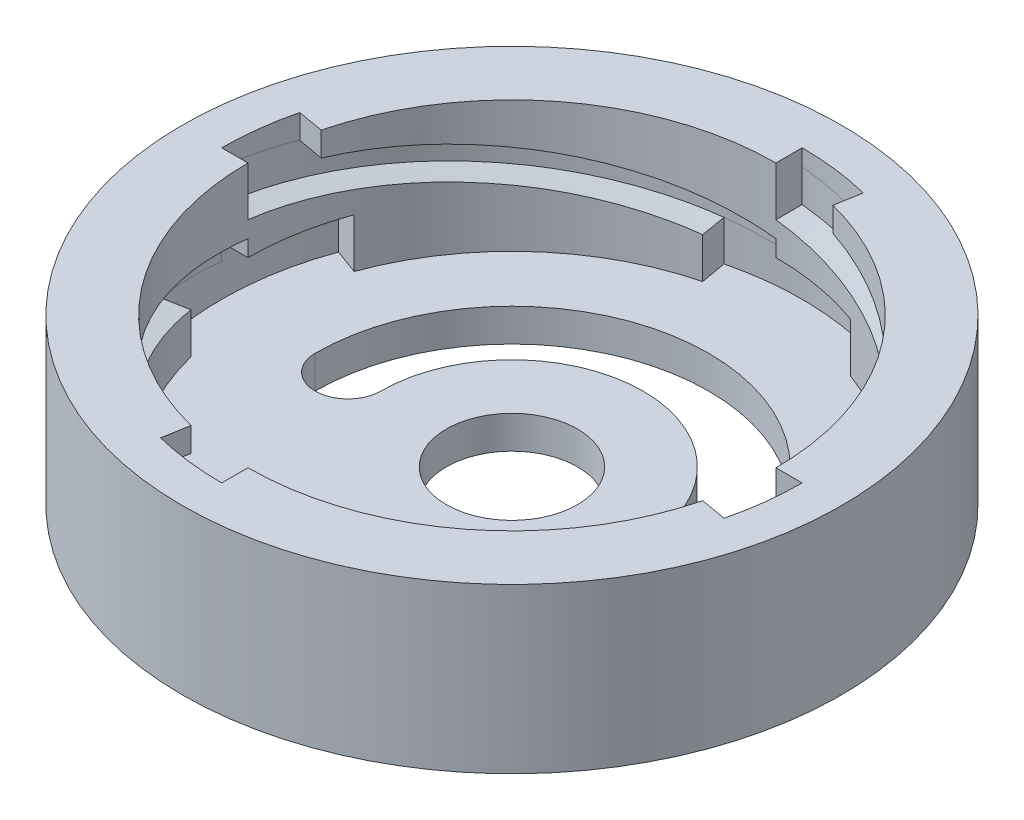
SolidWorks part; units mm, degrees
ref_plane "Front Plane" through (0, 0, 0) normal (0, 0, 1) x (1, 0, 0)
ref_plane "Top Plane" through (0, 0, 0) normal (0, 1, 0) x (1, 0, 0)
ref_plane "Right Plane" through (0, 0, 0) normal (1, 0, 0) x (0, 0, -1)
sketch "Sketch1" plane through (0, 0, 0) normal (0, 1, 0) x (1, 0, 0)
  line L0 (-10, 0) -> (10, 0) construction
  circle A0 centre (0, 0) radius 16.1
  circle A1 centre (0, 0) radius 4
  arc A2 (-10, 0) -> (10, 0) centre (0, 0) cw construction
  arc A3 (12, 0) -> (-12, 0) centre (0, 0) ccw
  arc A4 (8, 0) -> (-8, 0) centre (0, 0) ccw
  arc A5 (8, 0) -> (12, 0) centre (10, 0) ccw
  arc A6 (-12, 0) -> (-8, 0) centre (-10, 0) ccw
  point P6 (0, 10)
  dimension "D1" = 32.2
  dimension "D2" = 2
  dimension "D3" = 8
  dimension "D4" = 10
extrude "Boss-Extrude1" add sketch "Sketch1" along normal blind 2
sketch "Sketch2" plane through (0, 0, 0) normal (0, 1, 0) x (1, 0, 0)
  circle A0 centre (0, 0) radius 20.1
  circle A1 centre (0, 0) radius 16.1
  circle A2 centre (0, 0) radius 16.1
  dimension "D1" = 0
  dimension "D2" = 4
extrude "Boss-Extrude2" add sketch "Sketch2" along normal blind 10
sketch "Sketch3" plane through (0, 10, 0) normal (0, 1, 0) x (1, 0, 0)
  circle A0 centre (0, 0) radius 16.1 construction
  circle A1 centre (0, 0) radius 16.1
ref_plane "Plane1" through (0, 8, 0) normal (0, 1, 0) x (1, 0, 0)
sketch "Sketch34" plane through (0, 8, 0) normal (0, 1, 0) x (1, 0, 0)
  circle A0 centre (0, 0) radius 16.1 construction
  circle A1 centre (0, 0) radius 16.1
curve "Helix/Spiral2" pitch 12 height 3 turns 0.25
sketch "Sketch35" plane through (0, 0, 0) normal (0, 0, 1) x (1, 0, 0)
  line L1 (-17.7, 7) -> (-14.5, 7)
  line L2 (-17.7, 7) -> (-17.7, 9)
  line L3 (-17.7, 9) -> (-14.5, 9)
  line L4 (-14.5, 7) -> (-14.5, 9)
  line L5 (-17.7, 7) -> (-14.5, 9) construction
  line L6 (-17.7, 9) -> (-14.5, 7) construction
  line L7 (-16.1, 10) -> (-16.1, 2) construction
  line L8 (23.65, 8) -> (-23.65, 8) construction
  spline S1 degree 3 poles (-16.1, 8) (-16.1, 7.7516) (-15.2622, 7.2493) (-11.6792, 6.5) (-6.3277, 5.7507) (-2.0942, 5.2484) (0, 5) knots 0 0 0 0 0.25 0.5 0.75 1 1 1 1 construction
  point P0 (-16.1, 8)
  dimension "D1" = 2
  dimension "D2" = 1.6
sweep "Cut-Sweep2" cut profiles "Sketch35" path "Helix/Spiral2"
pattern_circular "CirPattern3" count 4 over 360 about axis through (0, 2, 0) along (0, -1, 0) of "Cut-Sweep2"
sketch "Sketch36" plane through (0, 10, 0) normal (0, 1, 0) x (1, 0, 0)
  line L16 (-16.1, 0) -> (-17.7, 0)
  line L17 (-17.7, 0) -> (-16.1, 0) construction
  line L18 (-15.6031, 3.969) -> (-17.1828, 4.2476)
  circle A5 centre (0, 0) radius 16.1 construction
  circle A7 centre (0, 0) radius 16.1 construction
  circle A8 centre (0, 0) radius 16.1
  circle A9 centre (0, 0) radius 17.7
  dimension "D1" = 10
  dimension "D2" = 4
extrude "Cut-Extrude1" cut sketch "Sketch36" against normal blind 2
pattern_circular "CirPattern4" count 4 over 360 about axis through (0, 0, 0) along (0, 1, 0) of "Cut-Extrude1"
sketch "Sketch37" plane through (0, 2, 0) normal (0, 1, 0) x (1, 0, 0)
  line L1 (-16.6326, 6.0538) -> (-15.1291, 5.5065)
  line L2 (-16.1, 0) -> (-17.7, 0) construction
  line L3 (-16.1, 0) -> (-17.7, 0)
  line L4 (-17.1828, -4.2476) -> (-15.6031, -3.969)
  circle A0 centre (0, 0) radius 16.1 construction
  circle A1 centre (0, 0) radius 16.1
  circle A3 centre (0, 0) radius 17.7
  arc A4 (-16.1, 0) -> (-3.969, -15.6031) centre (0, 0) ccw construction
  dimension "D1" = 20
  dimension "D2" = 10
  dimension "D3" = 4
extrude "Cut-Extrude4" cut sketch "Sketch37" along normal blind 3
pattern_circular "CirPattern5" count 4 over 360 about axis through (0, 0, 0) along (0, 1, 0) of "Cut-Extrude4"
